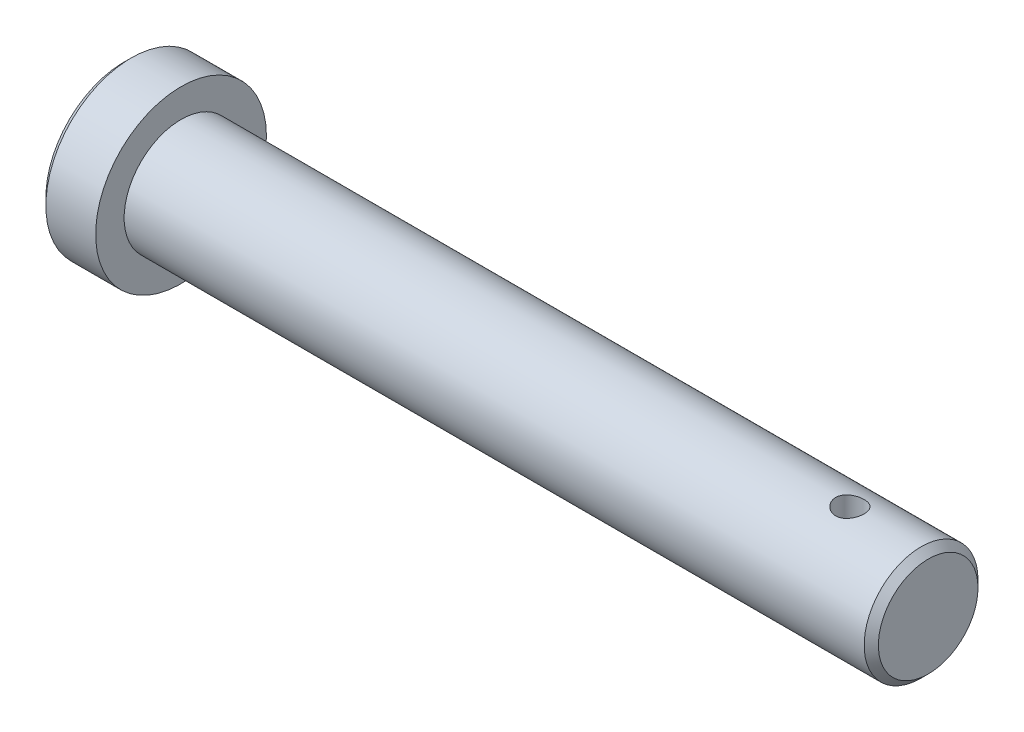
SolidWorks part; units mm, degrees
ref_plane "Front Plane" through (0, 0, 0) normal (0, 0, 1) x (1, 0, 0)
ref_plane "Top Plane" through (0, 0, 0) normal (0, 1, 0) x (1, 0, 0)
ref_plane "Right Plane" through (0, 0, 0) normal (1, 0, 0) x (0, 0, -1)
sketch "Sketch1" plane through (0, 0, 0) normal (1, 0, 0) x (0, 0, -1)
  circle A0 centre (0, 0) radius 12
  dimension "D1" = 24
extrude "Boss-Extrude1" add sketch "Sketch1" along normal blind 8
chamfer "Chamfer1" distance 1 angle 45 1 edges at (0, 0, -12)
sketch "Sketch2" plane through (8, 0, 0) normal (1, 0, 0) x (0, 0, -1)
  circle A0 centre (0, 0) radius 8
  dimension "D1" = 16
extrude "Boss-Extrude2" add sketch "Sketch2" along normal blind 105
chamfer "Chamfer2" distance 1 angle 45 1 edges at (113, 0, -8)
sketch "Sketch3" plane through (0, 0, 0) normal (0, 1, 0) x (1, 0, 0)
  line L0 (8, -12) -> (8, 12) construction
  circle A0 centre (102, 0) radius 2
  dimension "D1" = 4
  dimension "D2" = 94
extrude "Cut-Extrude1" cut sketch "Sketch3" against normal mid plane 105
